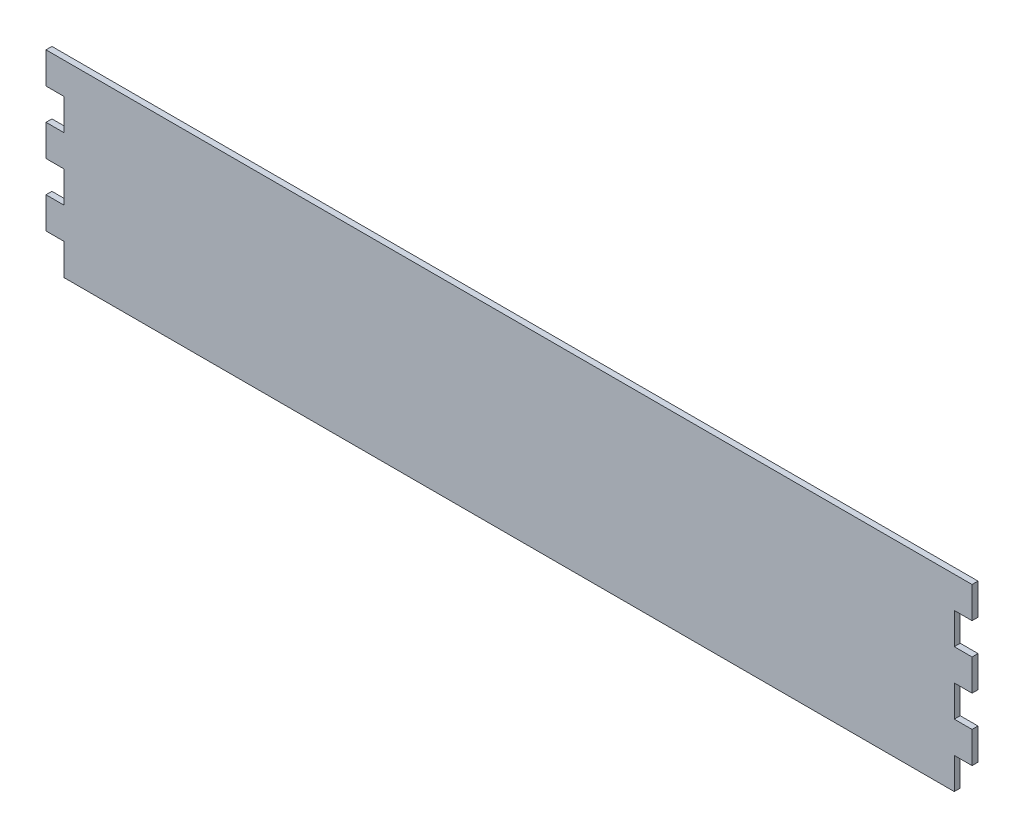
SolidWorks part; units mm, degrees
ref_plane "Face" through (0, 0, 0) normal (0, 0, 1) x (1, 0, 0)
ref_plane "Dessus" through (0, 0, 0) normal (0, 1, 0) x (1, 0, 0)
ref_plane "Droite" through (0, 0, 0) normal (1, 0, 0) x (0, 0, -1)
sketch "Esquisse1" plane through (0, 0, 0) normal (0, 0, 1) x (1, 0, 0)
  line L1 (-63.9974, -108.6801) -> (236.0026, -108.6801)
  line L13 (86.0026, -45.2516) -> (86.0026, -119.2516) construction
  line L26 (242.0026, -45.2516) -> (242.0026, -55.823) construction
  line L28 (242.0026, -119.2516) -> (242.0026, -108.6801)
  line L29 (-69.9974, -119.2516) -> (242.0026, -119.2516)
  line L30 (-69.9974, -108.6801) -> (-69.9974, -119.2516)
  line L31 (-67.9974, -108.6801) -> (-69.9974, -108.6801)
  line L32 (-67.9974, -98.1087) -> (-67.9974, -108.6801)
  line L33 (-69.9974, -98.1087) -> (-67.9974, -98.1087)
  line L34 (-69.9974, -87.5373) -> (-69.9974, -98.1087)
  line L35 (-67.9974, -87.5373) -> (-69.9974, -87.5373)
  line L36 (-67.9974, -76.9658) -> (-67.9974, -87.5373)
  line L37 (-69.9974, -76.9658) -> (-67.9974, -76.9658)
  line L38 (-69.9974, -66.3944) -> (-69.9974, -76.9658)
  line L39 (-67.9974, -66.3944) -> (-69.9974, -66.3944)
  line L40 (-67.9974, -55.823) -> (-67.9974, -66.3944)
  line L41 (-69.9974, -55.823) -> (-67.9974, -55.823)
  line L42 (-69.9974, -45.2516) -> (-69.9974, -55.823)
  line L43 (242.0026, -45.2516) -> (-69.9974, -45.2516)
  line L44 (242.0026, -55.823) -> (242.0026, -45.2516)
  line L45 (240.0026, -55.823) -> (242.0026, -55.823)
  line L46 (240.0026, -66.3944) -> (240.0026, -55.823)
  line L47 (242.0026, -66.3944) -> (240.0026, -66.3944)
  line L48 (242.0026, -76.9658) -> (242.0026, -66.3944)
  line L49 (240.0026, -76.9658) -> (242.0026, -76.9658)
  line L50 (240.0026, -87.5373) -> (240.0026, -76.9658)
  line L51 (242.0026, -87.5373) -> (240.0026, -87.5373)
  line L52 (242.0026, -98.1087) -> (242.0026, -87.5373)
  line L53 (240.0026, -98.1087) -> (242.0026, -98.1087)
  line L54 (240.0026, -108.6801) -> (240.0026, -98.1087)
  line L55 (242.0026, -108.6801) -> (240.0026, -108.6801)
  line L71 (242.0026, -45.2516) -> (-69.9974, -45.2516)
  line L84 (242.0026, -98.1087) -> (240.0026, -98.1087) construction
  line L85 (242.0026, -66.3944) -> (242.0026, -76.9658) construction
  line L86 (242.0026, -76.9658) -> (240.0026, -76.9658) construction
  line L88 (242.0026, -87.5373) -> (242.0026, -98.1087) construction
  line L89 (240.0026, -87.5373) -> (242.0026, -87.5373) construction
  line L90 (240.0026, -66.3944) -> (242.0026, -66.3944) construction
  line L92 (242.0026, -45.2516) -> (242.0026, -55.823)
  line L93 (242.0026, -55.823) -> (236.0026, -55.823)
  line L94 (236.0026, -66.3944) -> (242.0026, -66.3944)
  line L95 (242.0026, -66.3944) -> (242.0026, -76.9658)
  line L96 (242.0026, -76.9658) -> (236.0026, -76.9658)
  line L97 (236.0026, -87.5373) -> (242.0026, -87.5373)
  line L98 (242.0026, -87.5373) -> (242.0026, -98.1087)
  line L99 (242.0026, -98.1087) -> (236.0026, -98.1087)
  line L102 (236.0026, -55.823) -> (236.0026, -66.3944)
  line L103 (236.0026, -108.6801) -> (236.0026, -98.1087)
  line L104 (236.0026, -87.5373) -> (236.0026, -76.9658)
  line L105 (242.0026, -55.823) -> (240.0026, -55.823) construction
  line L106 (236.0026, -99.2516) -> (236.0026, -139.2516) construction
  line L107 (-69.9974, -45.2516) -> (-69.9974, -55.823)
  line L108 (-69.9974, -55.823) -> (-63.9974, -55.823)
  line L109 (-63.9974, -55.823) -> (-63.9974, -66.3944)
  line L110 (-63.9974, -66.3944) -> (-69.9974, -66.3944)
  line L111 (-69.9974, -66.3944) -> (-69.9974, -76.9658)
  line L112 (-69.9974, -76.9658) -> (-63.9974, -76.9658)
  line L113 (-63.9974, -87.5373) -> (-63.9974, -76.9658)
  line L114 (-63.9974, -87.5373) -> (-69.9974, -87.5373)
  line L115 (-69.9974, -87.5373) -> (-69.9974, -98.1087)
  line L116 (-69.9974, -98.1087) -> (-63.9974, -98.1087)
  line L117 (-63.9974, -108.6801) -> (-63.9974, -98.1087)
  dimension "D1" = 0
extrude "Boss.-Extru.1" add sketch "Esquisse1" against normal blind 2
